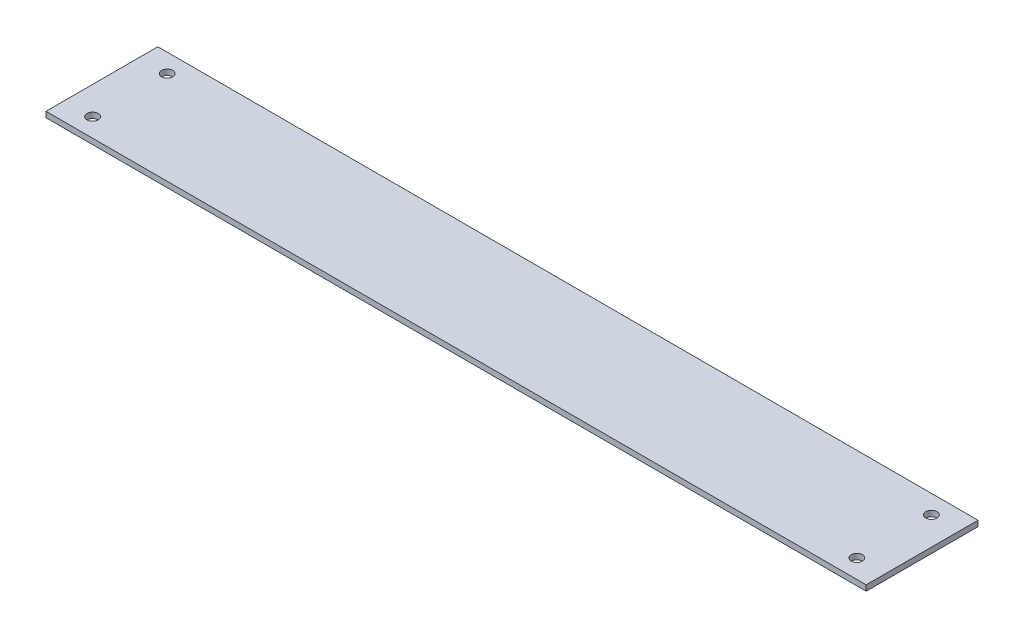
SolidWorks part; units mm, degrees
ref_plane "Front Plane" through (0, 0, 0) normal (0, 0, 1) x (1, 0, 0)
ref_plane "Top Plane" through (0, 0, 0) normal (0, 1, 0) x (1, 0, 0)
ref_plane "Right Plane" through (0, 0, 0) normal (1, 0, 0) x (0, 0, -1)
sketch "Sketch1" plane through (0, 0, 0) normal (0, 1, 0) x (1, 0, 0)
  line L0 (-110, 0) -> (-102.5, 0) construction
  line L1 (-110, 15) -> (110, 15)
  line L2 (-110, 15) -> (-110, -15)
  line L3 (-110, -15) -> (110, -15)
  line L4 (110, 15) -> (110, -15)
  line L5 (-110, 15) -> (110, -15) construction
  line L6 (-110, -15) -> (110, 15) construction
  line L7 (-102.5, 0) -> (-102.5, 10) construction
  line L8 (-102.5, 0) -> (-102.5, -10) construction
  line L9 (110, 0) -> (102.5, 0) construction
  line L10 (102.5, 0) -> (102.5, 10) construction
  circle A0 centre (-102.5, 10) radius 1.5
  circle A1 centre (-102.5, -10) radius 1.5
  circle A2 centre (102.5, 10) radius 1.5
  circle A3 centre (102.5, -10) radius 1.5
  point P0 (0, 0)
extrude "Boss-Extrude1" add sketch "Sketch1" along normal blind 1.5
